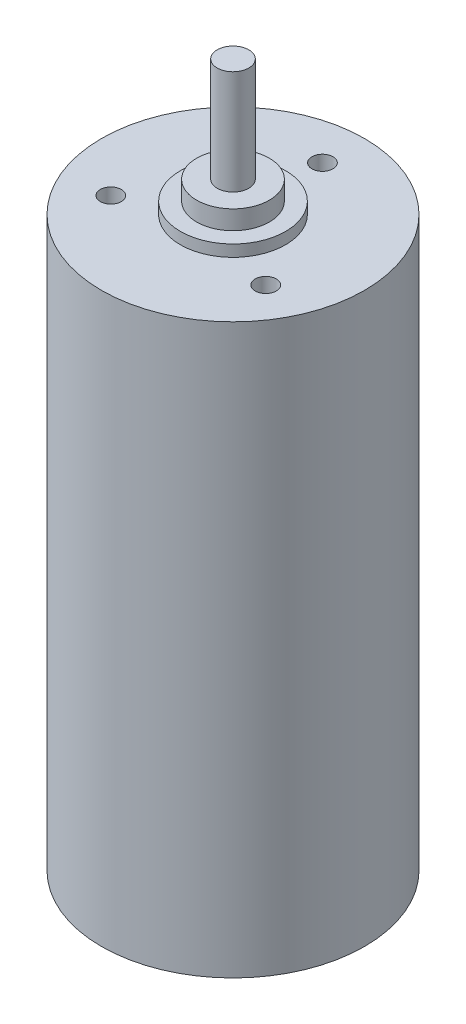
SolidWorks part; units mm, degrees
material "Custom Plastic"
ref_plane "Front Plane" through (0, 0, 0) normal (0, 0, 1) x (1, 0, 0)
ref_plane "Top Plane" through (0, 0, 0) normal (0, 1, 0) x (1, 0, 0)
ref_plane "Right Plane" through (0, 0, 0) normal (1, 0, 0) x (0, 0, -1)
sketch "Sketch1" plane through (0, 0, 0) normal (0, 1, 0) x (1, 0, 0)
  circle A0 centre (0, 0) radius 12.5
  dimension "D1" = 25
extrude "Boss-Extrude1" add sketch "Sketch1" along normal blind 54
sketch "Sketch2" plane through (0, 54, 0) normal (0, 1, 0) x (1, 0, 0)
  circle A0 centre (0, 0) radius 5
  dimension "D1" = 10
extrude "Boss-Extrude2" add sketch "Sketch2" along normal blind 1.1
sketch "Sketch3" plane through (0, 55.1, 0) normal (0, 1, 0) x (1, 0, 0)
  circle A0 centre (0, 0) radius 3.4552
extrude "Boss-Extrude3" add sketch "Sketch3" along normal blind 1.8
sketch "Sketch4" plane through (0, 56.9, 0) normal (0, 1, 0) x (1, 0, 0)
  circle A0 centre (0, 0) radius 1.5
  dimension "D1" = 3
extrude "Boss-Extrude4" add sketch "Sketch4" along normal blind 9.9
sketch "Sketch5" plane through (0, 54, 0) normal (0, 1, 0) x (1, 0, 0)
  line L0 (0, 12.5) -> (0, -12.5) construction
  line L1 (0, 0) -> (-10.8253, -6.25) construction
  line L2 (0, 0) -> (10.8253, -6.25) construction
  circle A0 centre (0, 0) radius 12.5 construction
  circle A1 centre (0, 0) radius 8.5
  point P10 (0, 8.5)
  point P11 (-7.3612, -4.25)
  point P12 (7.3612, -4.25)
  dimension "D2" = 17
  dimension "D1" = 60
hole_wizard "Ø2.0mm Dowel Hole1" positions "Sketch7" profile "Sketch6" hole size "Ø2.0" standard "ANSI Metric"
sketch "Sketch7" plane through (0, 54, 0) normal (0, 1, 0) x (1, 0, 0)
  point P0 (-7.3612, -4.25)
  point P3 (0, 8.5)
  point P6 (7.3612, -4.25)
sketch "Sketch6" plane through (-7.3612, 54, 4.25) normal (1, 0, 0) x (0, 0, 1)
  line L0 (0, 0) -> (0, 3.5009)
  line L1 (0, 3.5009) -> (1, 2.9)
  line L2 (1, 2.9) -> (1, 0)
  line L5 (1, 0) -> (0, 0)
  line L10 (0, 3.5009) -> (-1, 2.9) construction
  line L11 (0, -6.35) -> (0, 107.95) construction
  dimension "Hole Dia." = 2
  dimension "Hole Depth" = 2.9
  dimension "Drill Angle" = 118
